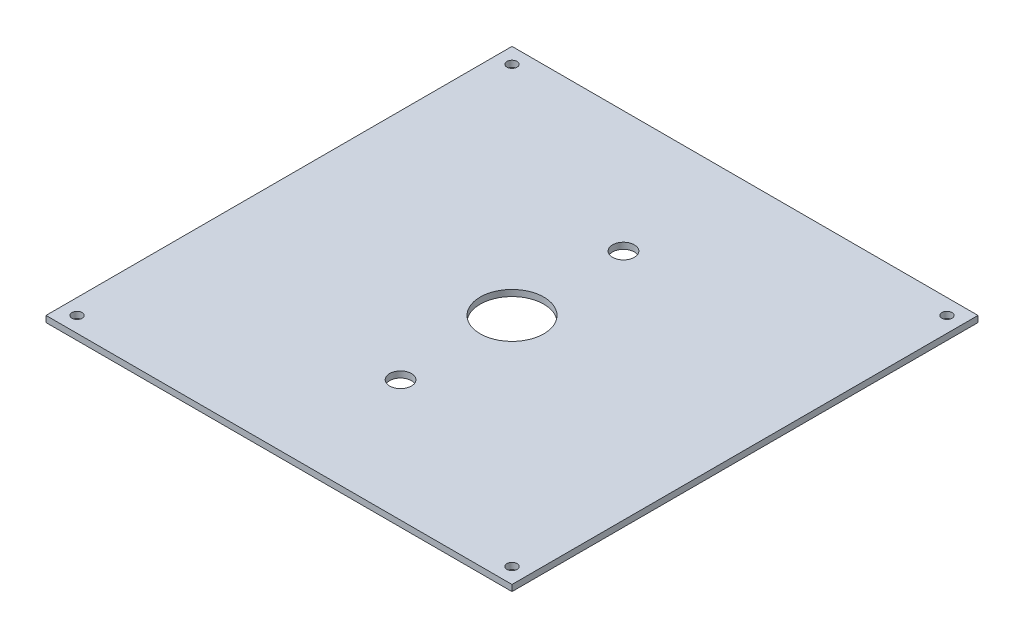
SolidWorks part; units mm, degrees
ref_plane "Front Plane" through (0, 0, 0) normal (0, 0, 1) x (1, 0, 0)
ref_plane "Top Plane" through (0, 0, 0) normal (0, 1, 0) x (1, 0, 0)
ref_plane "Right Plane" through (0, 0, 0) normal (1, 0, 0) x (0, 0, -1)
sketch "Sketch1" plane through (0, 0, 0) normal (0, 1, 0) x (1, 0, 0)
  line L1 (150, 150) -> (-150, 150)
  line L2 (150, 150) -> (150, -150)
  line L3 (150, -150) -> (-150, -150)
  line L4 (-150, 150) -> (-150, -150)
  line L5 (150, 150) -> (-150, -150) construction
  line L6 (150, -150) -> (-150, 150) construction
  point P0 (0, 0)
  dimension "D1" = 300
extrude "Boss-Extrude1" add sketch "Sketch1" along normal blind 4
sketch "Sketch2" plane through (0, 4, 0) normal (0, 1, 0) x (1, 0, 0)
  line L0 (-150, 150) -> (150, -150) construction
  line L1 (-150, 0) -> (150, 0) construction
  line L2 (-150, 150) -> (-150, -150) construction
  line L3 (150, -150) -> (150, 150) construction
  line L4 (0, 150) -> (0, -150) construction
  line L5 (150, 150) -> (-150, 150) construction
  line L6 (-150, -150) -> (150, -150) construction
  circle A0 centre (-140, 140) radius 3.25
  circle A1 centre (140, 140) radius 3.25
  circle A2 centre (140, -140) radius 3.25
  circle A3 centre (-140, -140) radius 3.25
  dimension "D1" = 6.5
  dimension "D2" = 280
extrude "Cut-Extrude1" cut sketch "Sketch2" against normal up to next
sketch "Sketch3" plane through (0, 4, 0) normal (0, 1, 0) x (1, 0, 0)
  circle A0 centre (0, 0) radius 20.5
  dimension "D1" = 41
extrude "Cut-Extrude2" cut sketch "Sketch3" against normal up to next
sketch "Sketch4" plane through (0, 4, 0) normal (0, 1, 0) x (1, 0, 0)
  line L0 (0, 150) -> (0, -150) construction
  line L1 (150, 150) -> (-150, 150) construction
  line L2 (-150, -150) -> (150, -150) construction
  line L3 (-150, 0) -> (150, 0) construction
  line L4 (-150, 150) -> (-150, -150) construction
  line L5 (150, -150) -> (150, 150) construction
  circle A0 centre (0, 71.75) radius 7
  circle A1 centre (0, -71.75) radius 7
  dimension "D1" = 14
  dimension "D2" = 143.5
extrude "Cut-Extrude3" cut sketch "Sketch4" against normal up to next
